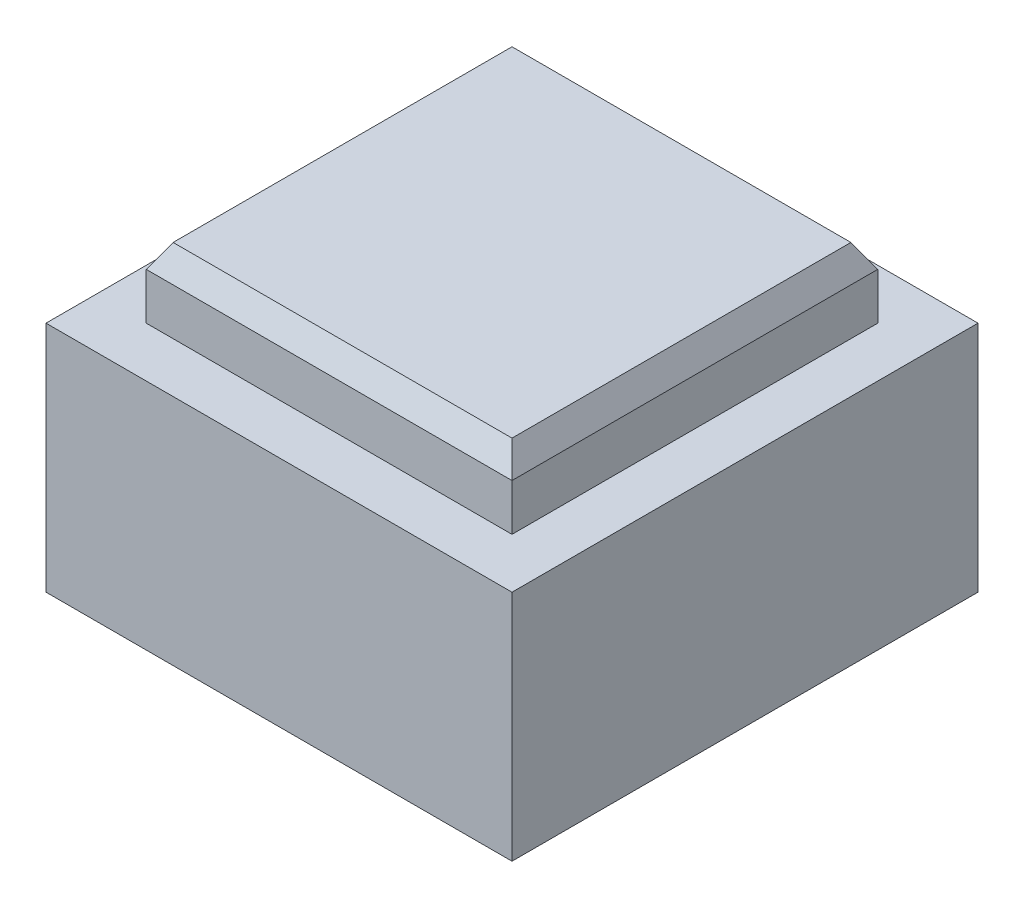
SolidWorks part; units mm, degrees
ref_plane "Спереди" through (0, 0, 0) normal (0, 0, 1) x (1, 0, 0)
ref_plane "Сверху" through (0, 0, 0) normal (0, 1, 0) x (1, 0, 0)
ref_plane "Справа" through (0, 0, 0) normal (1, 0, 0) x (0, 0, -1)
sketch "Sketch1" plane through (0, 0, 0) normal (0, 1, 0) x (1, 0, 0)
  line L1 (10, -10) -> (-10, -10)
  line L2 (10, -10) -> (10, 10)
  line L3 (10, 10) -> (-10, 10)
  line L4 (-10, -10) -> (-10, 10)
  line L5 (10, -10) -> (-10, 10) construction
  line L6 (10, 10) -> (-10, -10) construction
  point P0 (0, 0)
  dimension "D1" = 20
extrude "Boss-Extrude1" add sketch "Sketch1" along normal blind 10
sketch "Sketch2" plane through (0, 10, 0) normal (0, 1, 0) x (1, 0, 0)
  line L1 (7.85, -7.85) -> (-7.85, -7.85)
  line L2 (7.85, -7.85) -> (7.85, 7.85)
  line L3 (7.85, 7.85) -> (-7.85, 7.85)
  line L4 (-7.85, -7.85) -> (-7.85, 7.85)
  line L5 (7.85, -7.85) -> (-7.85, 7.85) construction
  line L6 (7.85, 7.85) -> (-7.85, -7.85) construction
  point P0 (0, 0)
  dimension "D1" = 15.7
extrude "Boss-Extrude2" add sketch "Sketch2" along normal blind 3
chamfer "Chamfer1" distance 1 angle 30 4 edges at (0, 13, 7.85) (7.85, 13, 0) (0, 13, -7.85) (-7.85, 13, 0)
sketch "Sketch3" plane through (0, 0, 0) normal (0, -1, 0) x (1, 0, 0)
  line L0 (-10, 10) -> (10, 10) construction
  line L1 (-3.7, 6.4086) -> (-7.4, 0)
  line L2 (-7.4, 0) -> (-3.7, -6.4086)
  line L3 (-3.7, -6.4086) -> (3.7, -6.4086)
  line L4 (3.7, -6.4086) -> (7.4, 0)
  line L5 (7.4, 0) -> (3.7, 6.4086)
  line L6 (3.7, 6.4086) -> (-3.7, 6.4086)
  circle A0 centre (0, 0) radius 7.4 construction
  dimension "D1" = 14.8
extrude "Cut-Extrude1" cut sketch "Sketch3" against normal blind 8
chamfer "Chamfer2" distance 1 angle 70 6 edges at (-5.55, 0, -3.2043) (0, 0, -6.4086) (5.55, 0, -3.2043) (5.55, 0, 3.2043) (0, 0, 6.4086) (-5.55, 0, 3.2043)
